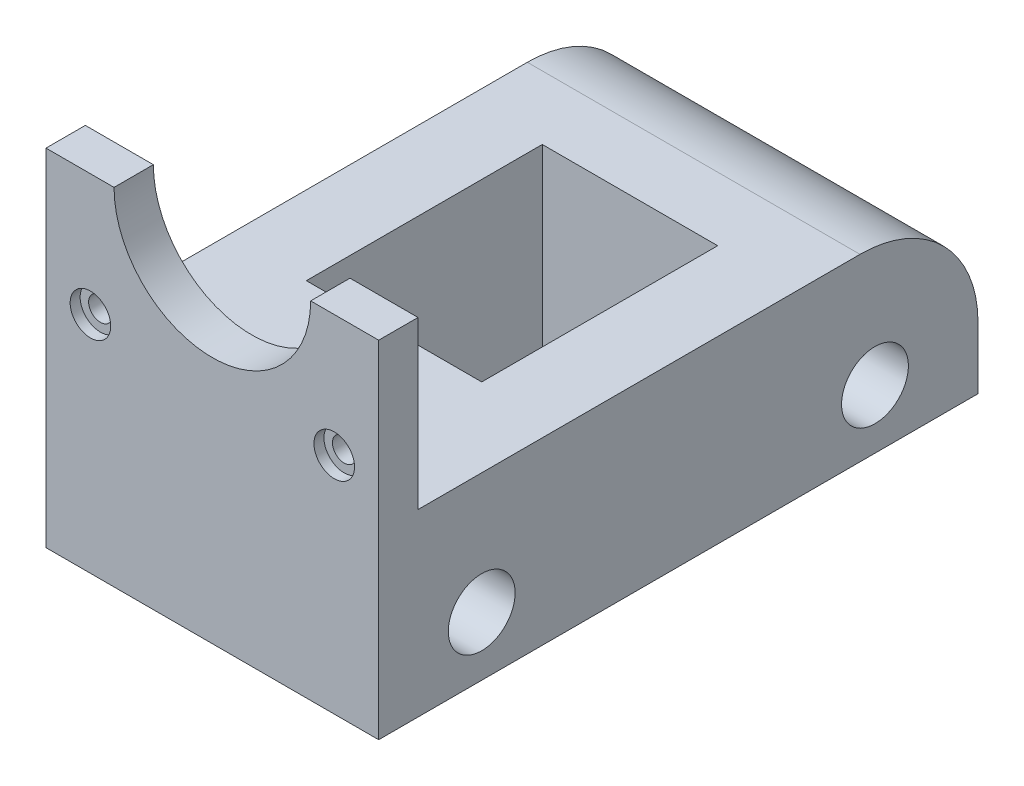
SolidWorks part; units mm, degrees
ref_plane "Front Plane" through (0, 0, 0) normal (0, 0, 1) x (1, 0, 0)
ref_plane "Top Plane" through (0, 0, 0) normal (0, 1, 0) x (1, 0, 0)
ref_plane "Right Plane" through (0, 0, 0) normal (1, 0, 0) x (0, 0, -1)
sketch "Sketch2" plane through (0, 0, 0) normal (0, 1, 0) x (1, 0, 0)
  line L1 (-19.1815, 10.163) -> (23.1185, 10.163)
  line L2 (-19.1815, 10.163) -> (-19.1815, -66.037)
  line L3 (-19.1815, -66.037) -> (23.1185, -66.037)
  line L4 (23.1185, 10.163) -> (23.1185, -66.037)
  dimension "D1" = 42.3
  dimension "D2" = 76.2
extrude "Boss-Extrude1" add sketch "Sketch2" along normal blind 15
sketch "Sketch5" plane through (0, 0, 66.037) normal (0, 0, 1) x (1, 0, 0)
  line L0 (23.1185, 15) -> (23.1185, 0) construction
  line L1 (-19.1815, 15) -> (23.1185, 15)
  line L2 (-19.1815, 15) -> (-19.1815, 57.3)
  line L3 (-19.1815, 57.3) -> (23.1185, 57.3)
  line L4 (23.1185, 15) -> (23.1185, 57.3)
  dimension "D1" = 42.3
extrude "Mounting" add sketch "Sketch5" against normal blind 5
sketch "Sketch6" plane through (0, 0, 66.037) normal (0, 0, 1) x (1, 0, 0)
  line L0 (23.1185, 57.3) -> (23.1185, 0) construction
  line L1 (-19.1815, 57.3) -> (23.1185, 57.3)
  line L2 (-19.1815, 57.3) -> (-19.1815, 15)
  line L3 (-19.1815, 15) -> (23.1185, 15) construction
  line L4 (23.1185, 57.3) -> (23.1185, 15)
  line L5 (-19.1815, 36.15) -> (23.1185, 36.15)
  line L6 (-19.1815, 57.3) -> (-19.1815, 36.15)
  line L7 (23.1185, 36.15) -> (23.1185, 57.3)
  line L8 (-19.1815, 0) -> (23.1185, 0) construction
  circle A0 centre (1.9685, 36.15) radius 12.5
  line M7 (23.1185, 57.3) -> (-19.1815, 57.3)
  line M8 (-19.1815, 57.3) -> (-19.1815, 0)
  dimension "D2" = 25
  dimension "D1" = 42.3
  dimension "D3" = 36.15
extrude "Pully Hole" cut sketch "Sketch6" against normal through all contours L5 L4 M8 M7 | A0
sketch "Sketch8" plane through (0, 0, 66.037) normal (0, 0, 1) x (1, 0, 0)
  line L0 (1.9685, 15) -> (1.9685, 36.15) construction
  line L5 (-10.5315, 36.15) -> (-19.1815, 36.15)
  line L6 (23.1185, 36.15) -> (14.4685, 36.15)
  line L7 (23.1185, 15) -> (23.1185, 36.15)
  line L8 (-19.1815, 15) -> (23.1185, 15)
  line L9 (-19.1815, 36.15) -> (-19.1815, 15)
  line L10 (-10.5315, 36.15) -> (-19.1815, 36.15)
  line L11 (23.1185, 36.15) -> (14.4685, 36.15)
  line L12 (23.1185, 15) -> (23.1185, 36.15)
  line L13 (-19.1815, 15) -> (23.1185, 15)
  line L14 (-19.1815, 36.15) -> (-19.1815, 15)
  circle A0 centre (-13.5315, 20.65) radius 1.5
  arc A1 (-10.5315, 36.15) -> (14.4685, 36.15) centre (1.9685, 36.15) ccw
  arc A2 (-10.5315, 36.15) -> (14.4685, 36.15) centre (1.9685, 36.15) ccw
  circle A3 centre (17.4685, 20.65) radius 1.5
  dimension "D4" = 3
  dimension "D2" = 5.65
  dimension "D3" = 5.65
  dimension "D1" = 0
extrude "M3" cut sketch "Sketch8" against normal through all contours A0 | A3
sketch "Sketch9" plane through (0, 0, 66.037) normal (0, 0, 1) x (1, 0, 0)
  line L0 (1.9685, 23.65) -> (1.9685, 15.8341) construction
  circle A0 centre (-13.5315, 20.65) radius 2.58
  arc A1 (-10.5315, 36.15) -> (14.4685, 36.15) centre (1.9685, 36.15) ccw construction
  circle A2 centre (17.4685, 20.65) radius 2.58
  dimension "D1" = 5.16
extrude "Screw Tops" cut sketch "Sketch9" against normal blind 1.27
sketch "Sketch11" plane through (0, 0, 0) normal (0, -1, 0) x (1, 0, 0)
  line L0 (-19.1815, 27.937) -> (23.1185, 27.937) construction
  line L1 (-19.1815, -10.163) -> (-19.1815, 66.037) construction
  line L2 (23.1185, 66.037) -> (23.1185, -10.163) construction
  line L4 (-9.1815, 12.937) -> (13.1185, 12.937)
  line L5 (-9.1815, 12.937) -> (-9.1815, 42.937)
  line L6 (-9.1815, 42.937) -> (13.1185, 42.937)
  line L7 (13.1185, 12.937) -> (13.1185, 42.937)
  line L8 (-9.1815, 12.937) -> (13.1185, 42.937) construction
  line L9 (-9.1815, 42.937) -> (13.1185, 12.937) construction
  point P6 (1.9685, 27.937)
  dimension "D1" = 10
  dimension "D2" = 30
extrude "Cut-Extrude1" cut sketch "Sketch11" against normal through all
sketch "Sketch12" plane through (0, 0, 0) normal (0, -1, 0) x (1, 0, 0)
  line L0 (-9.1815, 42.937) -> (-9.1815, 12.937) construction
  line L1 (-9.1815, 12.937) -> (13.1185, 12.937) construction
  line L3 (13.1185, 42.937) -> (-9.1815, 42.937) construction
  line L4 (-19.1815, 66.037) -> (-19.1815, -10.163)
  line L5 (-19.1815, -10.163) -> (23.1185, -10.163)
  line L6 (23.1185, -10.163) -> (23.1185, 66.037)
  line L7 (23.1185, 66.037) -> (-19.1815, 66.037)
  line L8 (-19.1815, 66.037) -> (-19.1815, -10.163)
  line L9 (-19.1815, -10.163) -> (23.1185, -10.163)
  line L10 (23.1185, -10.163) -> (23.1185, 66.037)
  line L11 (23.1185, 66.037) -> (-19.1815, 66.037)
  line L12 (13.1185, 42.937) -> (-9.1815, 42.937)
  line L13 (-9.1815, 12.937) -> (13.1185, 12.937)
  line L14 (-9.1815, 42.937) -> (-9.1815, 12.937)
  line L15 (13.1185, 12.937) -> (13.1185, 42.937) construction
  line L16 (13.1185, 12.937) -> (13.1185, 42.937)
  dimension "D1" = 0
extrude "7.85 correction to match" add sketch "Sketch12" along normal blind 7.85
sketch "Sketch13" plane through (23.1185, 0, 0) normal (1, 0, 0) x (0, 0, -1)
  line L0 (-27.937, -7.85) -> (-27.937, 7.15) construction
  line L1 (10.163, -7.85) -> (-66.037, -7.85) construction
  line L2 (-27.937, -0.35) -> (-66.037, -0.35) construction
  line L3 (-66.037, 36.15) -> (-66.037, -7.85) construction
  circle A0 centre (-52.937, -0.35) radius 4.25
  circle A1 centre (-2.937, -0.35) radius 4.25
  dimension "D2" = 8.5
  dimension "D1" = 15
  dimension "D3" = 50
extrude "Cut-Extrude2" cut sketch "Sketch13" against normal through all
fillet "Fillet1" radius 15 1 edges at (1.9685, 15, -10.163)
